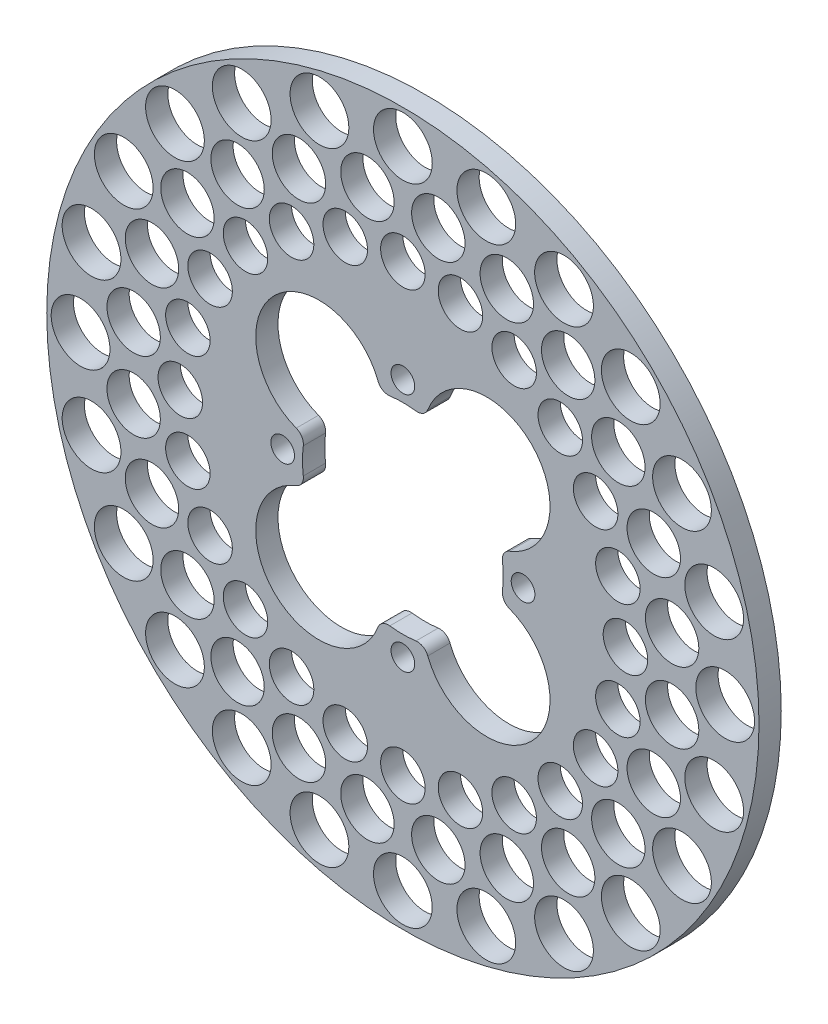
SolidWorks part; units mm, degrees
material "Plain Carbon Steel"
ref_plane "Front Plane" through (0, 0, 0) normal (0, 0, 1) x (1, 0, 0)
ref_plane "Top Plane" through (0, 0, 0) normal (0, 1, 0) x (1, 0, 0)
ref_plane "Right Plane" through (0, 0, 0) normal (1, 0, 0) x (0, 0, -1)
sketch "Sketch1" plane through (0, 0, 0) normal (0, 0, 1) x (1, 0, 0)
  line L0 (-34.29, 0) -> (34.29, 0) construction
  line L1 (0, 34.4997) -> (0, -34.0803) construction
  line L2 (0, 0) -> (20.486, -20.486) construction
  line L3 (0, 0) -> (-71.842, -71.842) construction
  line L4 (-27.94, 6.35) -> (-27.94, -6.35) construction
  line L5 (-27.94, 6.35) -> (-23.9419, 23.9419) construction
  line L6 (-27.94, -6.35) -> (-23.9419, -23.9419) construction
  line L7 (0, 0) -> (0, 63.5) construction
  line L8 (0, 0) -> (10.1119, 76.8072) construction
  circle A0 centre (0, 0) radius 34.29 construction
  circle A1 centre (0, 0) radius 101.6
  arc A2 (-28.409, -3.7272) -> (-28.409, 3.7272) centre (0, 0) cw
  circle A3 centre (0, 0) radius 41.91 construction
  arc A4 (-30.4174, 7.1036) -> (-7.1036, 30.4174) centre (-23.9419, 23.9419) cw
  arc A5 (-30.4174, -7.1036) -> (-7.1036, -30.4174) centre (-23.9419, -23.9419) ccw
  arc A6 (7.1036, 30.4174) -> (30.4174, 7.1036) centre (23.9419, 23.9419) cw
  arc A7 (3.7272, 28.409) -> (-3.7272, 28.409) centre (0, 0) ccw
  arc A8 (-3.7272, -28.409) -> (3.7272, -28.409) centre (0, 0) ccw
  arc A9 (28.409, 3.7272) -> (28.409, -3.7272) centre (0, 0) cw
  arc A10 (7.1036, -30.4174) -> (30.4174, -7.1036) centre (23.9419, -23.9419) ccw
  circle A11 centre (-34.29, 0) radius 3.429 construction
  arc A12 (3.7272, -28.409) -> (7.1036, -30.4174) centre (4.1402, -31.5571) cw
  arc A13 (-3.7272, -28.409) -> (-7.1036, -30.4174) centre (-4.1402, -31.5571) ccw
  arc A14 (-28.409, -3.7272) -> (-30.4174, -7.1036) centre (-31.5571, -4.1402) cw
  arc A15 (-30.4174, 7.1036) -> (-28.409, 3.7272) centre (-31.5571, 4.1402) cw
  arc A16 (-3.7272, 28.409) -> (-7.1036, 30.4174) centre (-4.1402, 31.5571) cw
  arc A17 (7.1036, 30.4174) -> (3.7272, 28.409) centre (4.1402, 31.5571) cw
  arc A18 (28.409, -3.7272) -> (30.4174, -7.1036) centre (31.5571, -4.1402) ccw
  arc A19 (28.409, 3.7272) -> (30.4174, 7.1036) centre (31.5571, 4.1402) cw
  circle A20 centre (0, 63.5) radius 6.35
  circle A21 centre (16.435, 61.3363) radius 6.35
  circle A22 centre (31.75, 54.9926) radius 6.35
  circle A23 centre (44.9013, 44.9013) radius 6.35
  circle A24 centre (54.9926, 31.75) radius 6.35
  circle A25 centre (61.3363, 16.435) radius 6.35
  circle A26 centre (63.5, 0) radius 6.35
  circle A27 centre (61.3363, -16.435) radius 6.35
  circle A28 centre (54.9926, -31.75) radius 6.35
  circle A29 centre (44.9013, -44.9013) radius 6.35
  circle A30 centre (31.75, -54.9926) radius 6.35
  circle A31 centre (16.435, -61.3363) radius 6.35
  circle A32 centre (0, -63.5) radius 6.35
  circle A33 centre (-16.435, -61.3363) radius 6.35
  circle A34 centre (-31.75, -54.9926) radius 6.35
  circle A35 centre (-44.9013, -44.9013) radius 6.35
  circle A36 centre (-54.9926, -31.75) radius 6.35
  circle A37 centre (-61.3363, -16.435) radius 6.35
  circle A38 centre (-63.5, 0) radius 6.35
  circle A39 centre (-61.3363, 16.435) radius 6.35
  circle A40 centre (-54.9926, 31.75) radius 6.35
  circle A41 centre (-44.9013, 44.9013) radius 6.35
  circle A42 centre (-31.75, 54.9926) radius 6.35
  circle A43 centre (-16.435, 61.3363) radius 6.35
  circle A44 centre (10.1119, 76.8072) radius 7.62
  circle A45 centre (29.6465, 71.5729) radius 7.62
  circle A46 centre (47.1607, 61.4611) radius 7.62
  circle A47 centre (61.4611, 47.1607) radius 7.62
  circle A48 centre (71.5729, 29.6465) radius 7.62
  circle A49 centre (76.8072, 10.1119) radius 7.62
  circle A50 centre (76.8072, -10.1119) radius 7.62
  circle A51 centre (71.5729, -29.6465) radius 7.62
  circle A52 centre (61.4611, -47.1607) radius 7.62
  circle A53 centre (47.1607, -61.4611) radius 7.62
  circle A54 centre (29.6465, -71.5729) radius 7.62
  circle A55 centre (10.1119, -76.8072) radius 7.62
  circle A56 centre (-10.1119, -76.8072) radius 7.62
  circle A57 centre (-29.6465, -71.5729) radius 7.62
  circle A58 centre (-47.1607, -61.4611) radius 7.62
  circle A59 centre (-61.4611, -47.1607) radius 7.62
  circle A60 centre (-71.5729, -29.6465) radius 7.62
  circle A61 centre (-76.8072, -10.1119) radius 7.62
  circle A62 centre (-76.8072, 10.1119) radius 7.62
  circle A63 centre (-71.5729, 29.6465) radius 7.62
  circle A64 centre (-61.4611, 47.1607) radius 7.62
  circle A65 centre (-47.1607, 61.4611) radius 7.62
  circle A66 centre (-29.6465, 71.5729) radius 7.62
  circle A67 centre (-10.1119, 76.8072) radius 7.62
  circle A68 centre (0, 91.948) radius 8.382
  circle A69 centre (23.7979, 88.8149) radius 8.382
  circle A70 centre (45.974, 79.6293) radius 8.382
  circle A71 centre (65.0171, 65.0171) radius 8.382
  circle A72 centre (79.6293, 45.974) radius 8.382
  circle A73 centre (88.8149, 23.7979) radius 8.382
  circle A74 centre (91.948, 0) radius 8.382
  circle A75 centre (88.8149, -23.7979) radius 8.382
  circle A76 centre (79.6293, -45.974) radius 8.382
  circle A77 centre (65.0171, -65.0171) radius 8.382
  circle A78 centre (45.974, -79.6293) radius 8.382
  circle A79 centre (23.7979, -88.8149) radius 8.382
  circle A80 centre (0, -91.948) radius 8.382
  circle A81 centre (-23.7979, -88.8149) radius 8.382
  circle A82 centre (-45.974, -79.6293) radius 8.382
  circle A83 centre (-65.0171, -65.0171) radius 8.382
  circle A84 centre (-79.6293, -45.974) radius 8.382
  circle A85 centre (-88.8149, -23.7979) radius 8.382
  circle A86 centre (-91.948, 0) radius 8.382
  circle A87 centre (-88.8149, 23.7979) radius 8.382
  circle A88 centre (-79.6293, 45.974) radius 8.382
  circle A89 centre (-65.0171, 65.0171) radius 8.382
  circle A90 centre (-45.974, 79.6293) radius 8.382
  circle A91 centre (-23.7979, 88.8149) radius 8.382
  point P5 (0, 34.29)
  point P9 (34.29, 0)
  point P10 (0, -34.29)
  point P11 (-34.29, 0)
  point P12 (0, 0)
  point P20 (-27.94, 0)
  point P37 (6.35, -27.94)
  point P40 (-6.35, -27.94)
  point P49 (-6.35, 27.94)
  point P52 (6.35, 27.94)
  point P55 (27.94, -6.35)
  point P58 (27.94, 6.35)
  dimension "D1" = 203.2
  dimension "D2" = 83.82
  dimension "D3" = 7.62
  dimension "D5" = 27.94
  dimension "D7" = 6.858
  dimension "D9" = 3.175
  dimension "D10" = 63.5
  dimension "D12" = 77.47
  dimension "D15" = 91.948
  dimension "D6" = 45
  dimension "D8" = 12.7
  dimension "D13" = 7.5
  dimension "D4" = 4
  dimension "D11" = 24
  dimension "D14" = 24
  dimension "D16" = 24
extrude "Boss-Extrude1" add sketch "Sketch1" along normal blind 6.35
hole_wizard "1/4 Clearance Hole1" positions "3DSketch2" profile "Sketch3" hole size "1/4" standard "ANSI Inch"
sketch3d "3DSketch2"
  point P0 (0, 34.29, 6.35)
  point P2 (-34.29, 0, 6.35)
  point P4 (34.29, 0, 6.35)
  point P6 (0, -34.29, 6.35)
sketch "Sketch3" plane through (0, 34.29, 6.35) normal (1, 0, 0) x (0, -1, 0)
  line L0 (0, 0) -> (0, 11.6818)
  line L1 (0, 11.6818) -> (3.3782, 9.652)
  line L2 (3.3782, 9.652) -> (3.3782, 0)
  line L5 (3.3782, 0) -> (0, 0)
  line L10 (0, 11.6818) -> (-3.3782, 9.652) construction
  line L11 (0, -6.35) -> (0, 107.95) construction
  dimension "Hole Dia." = 6.7564
  dimension "Hole Depth" = 9.652
  dimension "Drill Angle" = 118
sketch "brakepad-path" plane through (0, 0, 6.35) normal (0, 0, 1) x (1, 0, 0)
  circle A0 centre (0, 0) radius 68.834 construction
  circle A1 centre (0, 0) radius 100.076 construction
